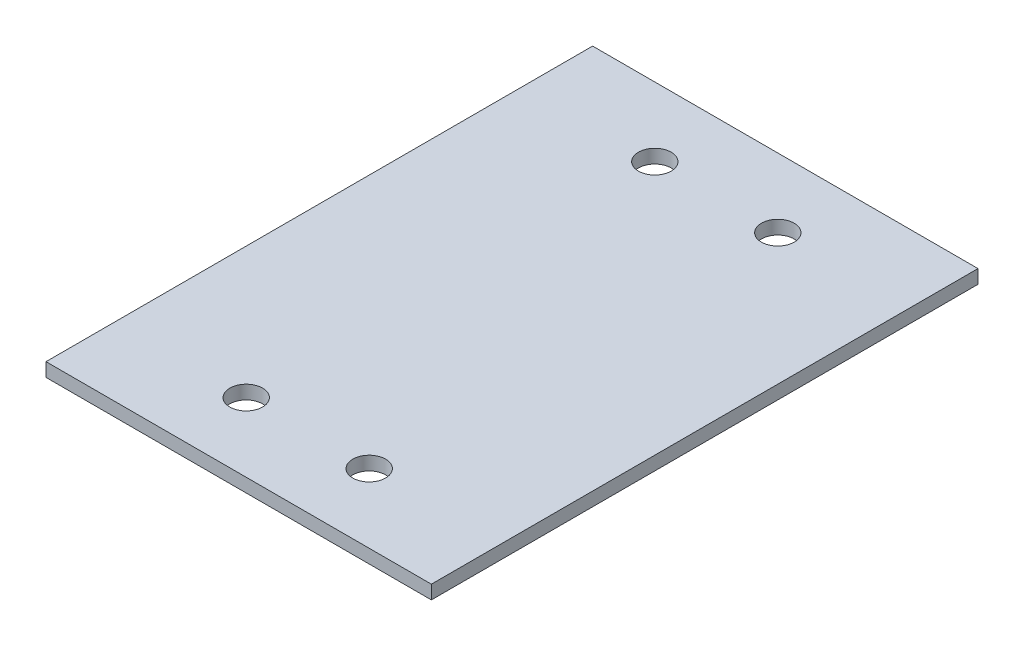
SolidWorks part; units mm, degrees
ref_plane "Front Plane" through (0, 0, 0) normal (0, 0, 1) x (1, 0, 0)
ref_plane "Top Plane" through (0, 0, 0) normal (0, 1, 0) x (1, 0, 0)
ref_plane "Right Plane" through (0, 0, 0) normal (1, 0, 0) x (0, 0, -1)
sketch "Sketch1" plane through (0, 0, 0) normal (0, 1, 0) x (1, 0, 0)
  line L0 (-22.5, 126.0226) -> (-22.5, 42.3148) construction
  line L1 (-70.5, -100) -> (70.5, -100)
  line L2 (-70.5, -100) -> (-70.5, 100)
  line L3 (-70.5, 100) -> (70.5, 100)
  line L4 (70.5, -100) -> (70.5, 100)
  line L5 (-70.5, -100) -> (70.5, 100) construction
  line L6 (-70.5, 100) -> (70.5, -100) construction
  line L7 (22.5, 150.3827) -> (22.5, -7.9607) construction
  line L8 (-22.5, 68.75) -> (55.2867, 68.75) construction
  line L9 (-175.1675, -68.75) -> (259.7266, -68.75) construction
  line L10 (-44.6767, 74.75) -> (295.6638, 74.75)
  line L11 (-246.4386, -74.75) -> (201.4293, -74.75)
  circle A4 centre (-22.5, 74.75) radius 6
  circle A5 centre (22.5, 74.75) radius 6
  circle A6 centre (-22.5, -74.75) radius 6
  circle A7 centre (22.5, -74.75) radius 6
  point P0 (0, 0)
  dimension "D1" = 200
  dimension "D2" = 141
  dimension "D3" = 48
  dimension "D4" = 48
  dimension "D5" = 137.5
extrude "Boss-Extrude1" add sketch "Sketch1" along normal blind 5
